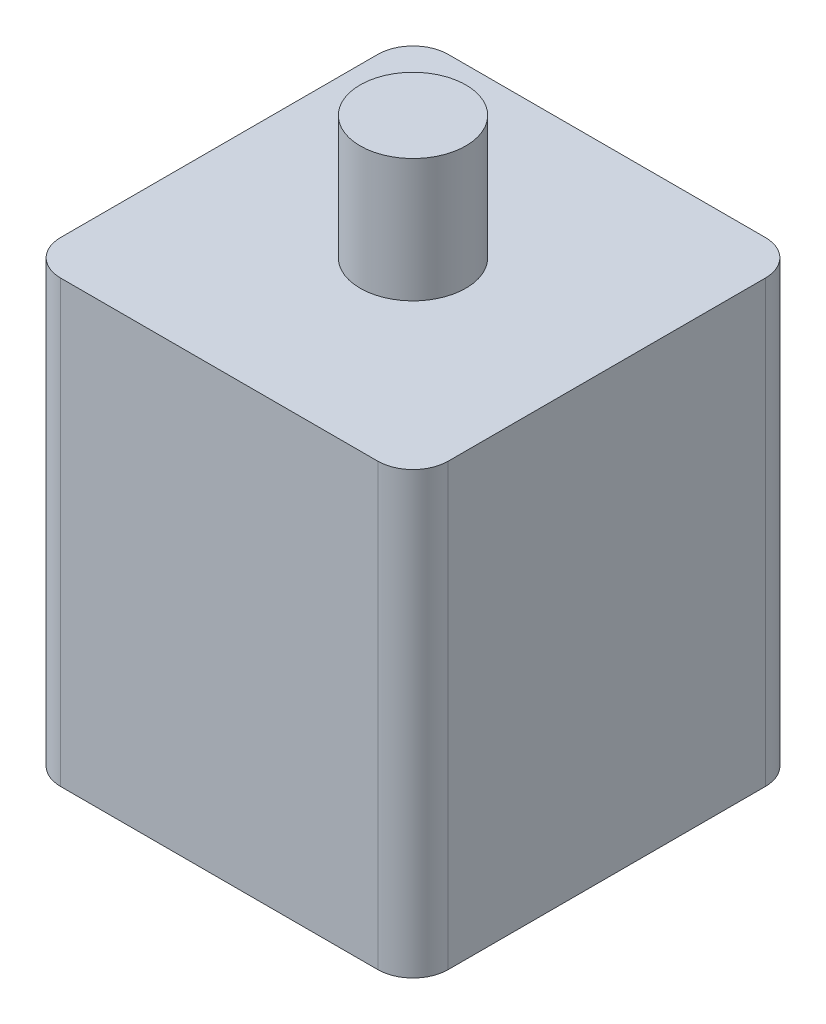
SolidWorks part; units mm, degrees
ref_plane "Front Plane" through (0, 0, 0) normal (0, 0, 1) x (1, 0, 0)
ref_plane "Top Plane" through (0, 0, 0) normal (0, 1, 0) x (1, 0, 0)
ref_plane "Right Plane" through (0, 0, 0) normal (1, 0, 0) x (0, 0, -1)
sketch "Sketch1" plane through (0, 0, 0) normal (0, 1, 0) x (1, 0, 0)
  line L1 (-9, -11) -> (9, -11)
  line L2 (-11, -9) -> (-11, 9)
  line L3 (-9, 11) -> (9, 11)
  line L4 (11, -9) -> (11, 9)
  line L5 (-11, -11) -> (11, 11) construction
  line L6 (-11, 11) -> (11, -11) construction
  circle A1 centre (0, 0) radius 6
  arc A2 (9, -11) -> (11, -9) centre (9, -9) ccw
  arc A3 (-9, -11) -> (-11, -9) centre (-9, -9) cw
  arc A4 (9, 11) -> (11, 9) centre (9, 9) cw
  arc A5 (-11, 9) -> (-9, 11) centre (-9, 9) cw
  dimension "D1" = 12
  dimension "D4" = 2
  dimension "D2" = 22
  dimension "D3" = 22
extrude "Boss-Extrude1" add sketch "Sketch1" along normal blind 25 contours A1 | A5 L2 A3 L1 A2 L4 A4 L3 A1
sketch "Sketch2" plane through (0, 25, 0) normal (0, 1, 0) x (1, 0, 0)
  circle A0 centre (0, 0) radius 3
  dimension "D1" = 6
extrude "Boss-Extrude2" add sketch "Sketch2" along normal blind 7
